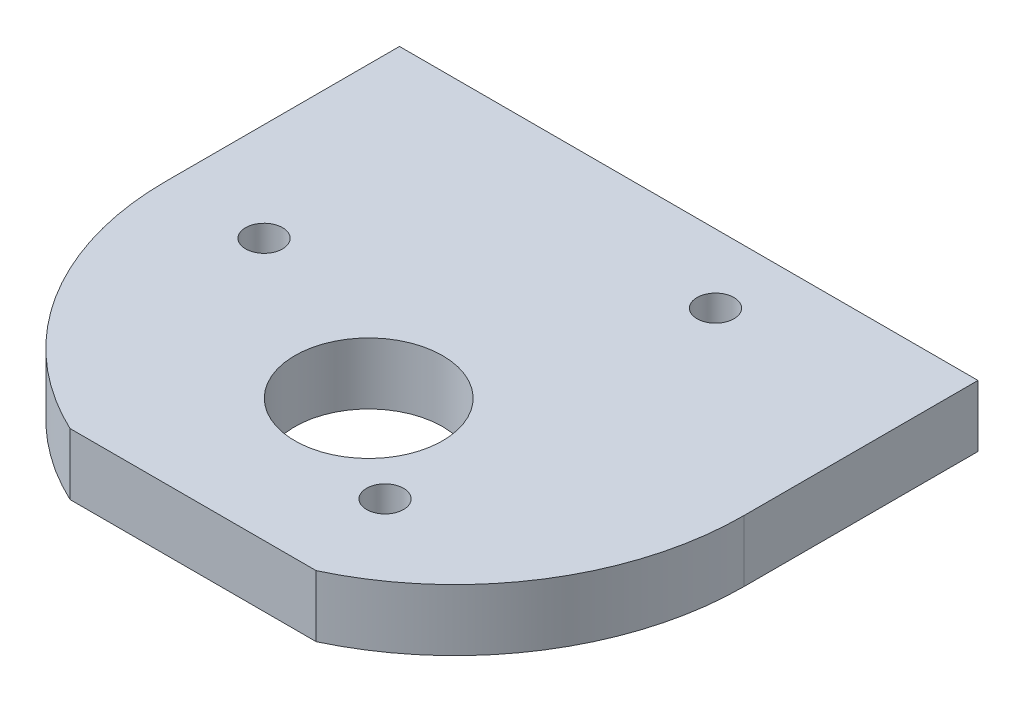
SolidWorks part; units mm, degrees
material "ｱｸﾘﾙ (中-上級の耐衝撃性)"
ref_plane "正面" through (0, 0, 0) normal (0, 0, 1) x (1, 0, 0)
ref_plane "平面" through (0, 0, 0) normal (0, 1, 0) x (1, 0, 0)
ref_plane "右側面" through (0, 0, 0) normal (1, 0, 0) x (0, 0, -1)
sketch "ｽｹｯﾁ1" plane through (0, 0, 0) normal (0, 0, 1) x (1, 0, 0)
  line L1 (-23.5, 2.5) -> (23.5, 2.5)
  line L2 (-23.5, 2.5) -> (-23.5, -2.5)
  line L3 (-23.5, -2.5) -> (23.5, -2.5)
  line L4 (23.5, 2.5) -> (23.5, -2.5)
  line L5 (-23.5, 2.5) -> (23.5, -2.5) construction
  line L6 (-23.5, -2.5) -> (23.5, 2.5) construction
  point P0 (0, 0)
  dimension "D1" = 5
  dimension "D2" = 47
extrude "ﾎﾞｽ - 押し出し1" add sketch "ｽｹｯﾁ1" along normal blind 19 contours L1 L4 L3 L2
sketch "ｽｹｯﾁ2" plane through (0, -2.5, 0) normal (0, -1, 0) x (1, 0, 0)
  line L0 (-23.5, 19) -> (23.5, 19) construction
  circle A0 centre (0, 19) radius 23.5
extrude "ﾎﾞｽ - 押し出し2" add sketch "ｽｹｯﾁ2" against normal blind 5
sketch "ｽｹｯﾁ3" plane through (0, -2.5, 0) normal (0, -1, 0) x (1, 0, 0)
  line L0 (-23.5, 19) -> (23.5, 19)
  line L1 (23.5, 19) -> (23.5, 0) construction
  line L2 (0, 19) -> (0, 26)
  line L3 (0, 19) -> (-15.5, 19)
  line L4 (0, 19) -> (7.75, 5.5766)
  line L5 (0, 19) -> (7.75, 32.4234)
  arc A0 (23.5, 19) -> (-23.5, 19) centre (0, 19) ccw construction
  circle A1 centre (0, 26) radius 6
  circle A2 centre (0, 19) radius 15.5
  circle A3 centre (-15.5, 19) radius 1.5
  circle A4 centre (7.75, 5.5766) radius 1.5
  circle A5 centre (7.75, 32.4234) radius 1.5
  dimension "D2" = 12
  dimension "D3" = 31
  dimension "D6" = 3
  dimension "D7" = 3
  dimension "D8" = 3
  dimension "D1" = 7
  dimension "D4" = 120
  dimension "D5" = 120
extrude "ｶｯﾄ - 押し出し1" cut sketch "ｽｹｯﾁ3" against normal blind 5 contours A1 | A5 | A3 | A4
sketch "ｽｹｯﾁ4" plane through (0, 0, 0) normal (0, 0, -1) x (-1, 0, 0)
  line L0 (0, 0) -> (-18, 0)
  line L1 (0, 0) -> (18, 0)
  dimension "D1" = 18
  dimension "D2" = 18
hole_wizard "M2.5x0.45 ねじ穴1" positions "ｽｹｯﾁ6" profile "ｽｹｯﾁ5" tap size "M2.5x0.45" standard "JIS"
sketch "ｽｹｯﾁ6" plane through (0, 0, 0) normal (0, 0, -1) x (-1, 0, 0)
  point P0 (18, 0)
  point P3 (-18, 0)
sketch "ｽｹｯﾁ5" plane through (-18, 0, 0) normal (1, 0, 0) x (0, 1, 0)
  line L0 (0, 0) -> (0, 7.8659)
  line L1 (0, 7.8659) -> (1.025, 7.25)
  line L2 (1.025, 7.25) -> (1.025, 0)
  line L5 (1.025, 0) -> (0, 0)
  line L10 (0, 7.8659) -> (-1.025, 7.25) construction
  line L11 (0, -6.35) -> (0, 107.95) construction
  dimension "ねじ下穴ﾄﾞﾘﾙ直径" = 2.05
  dimension "ねじ下穴ﾄﾞﾘﾙの深さ" = 7.25
  dimension "ﾄﾞﾘﾙ角度" = 118
cosmetic thread "穴のねじ山1" parameters "D1"=5, "D2"=2.5
cosmetic thread "穴のねじ山2" parameters "D1"=5, "D2"=2.5
sketch "ｽｹｯﾁ8" plane through (0, 2.5, 0) normal (0, 1, 0) x (1, 0, 0)
  line L0 (-13.8293, 0) -> (13.8293, 0)
  arc A1 (-13.8293, 0) -> (13.8293, 0) centre (0, -19) cw
extrude "ｶｯﾄ - 押し出し2" cut sketch "ｽｹｯﾁ8" against normal blind 5
sketch "ｽｹｯﾁ9" plane through (0, 2.5, 0) normal (0, 1, 0) x (1, 0, 0)
  line L0 (-10, -40.2662) -> (10, -40.2662)
  arc A0 (-23.5, -19) -> (23.5, -19) centre (0, -19) ccw construction
  arc A1 (-10, -40.2662) -> (10, -40.2662) centre (0, -19) ccw
extrude "ｶｯﾄ - 押し出し3" cut sketch "ｽｹｯﾁ9" against normal blind 5
